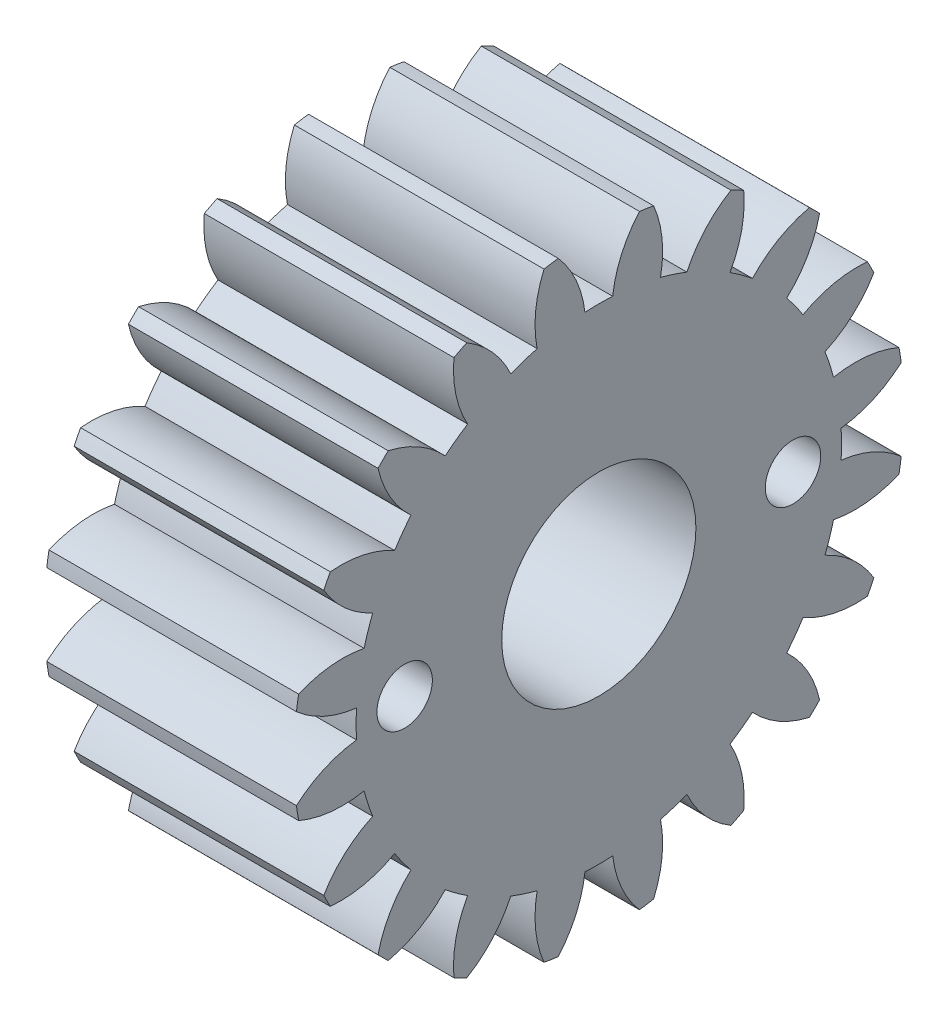
SolidWorks part; units mm, degrees
ref_plane "Plane1" through (0, 0, 0) normal (0, 0, 1) x (1, 0, 0)
ref_plane "Plane2" through (0, 0, 0) normal (0, 1, 0) x (1, 0, 0)
ref_plane "Plane3" through (0, 0, 0) normal (1, 0, 0) x (0, 0, -1)
other "Configuration Table"
sketch "HoldingSke" plane through (0, 0, 0) normal (0, 1, 0) x (1, 0, 0)
  line L0 (0, 0) -> (0.9397, -0.342)
  line L1 (-15, 0) -> (100, 0) construction
  line L2 (0, 0) -> (-2.1039, 2.3779)
  line L3 (0, 0) -> (-11.863, 4.5341)
  line L4 (0, 0) -> (8.1152, 2.9537)
  line L5 (0, 0) -> (-46.8476, -17.4728)
  line L6 (0, 0) -> (-4.1448, -2.7965)
  line L7 (-2.1039, 2.3779) -> (8.6586, 51.2059)
  line L8 (-76.2, 54.61) -> (-74.8, 54.61)
  line L9 (-71.009, 38.7566) -> (-53.1078, 45.2721)
  line L10 (-76.2, 71.12) -> (104.1128, 71.12)
  line L11 (0, 0) -> (-5, 0)
  line L12 (-76.2, 101.6) -> (-76.162, 101.6)
  line L13 (24.9733, 27.94) -> (52.9518, 28.4284)
  line L14 (24.9733, 27.94) -> (24.9743, 27.94)
  line L15 (24.9733, 27.94) -> (100.4006, 29.5858)
  line L16 (-63.627, -1) -> (-12.827, -1)
  circle A0 centre (0, 0) radius 4
  circle A1 centre (0, 0) radius 8.749
  circle A2 centre (0, 0) radius 37.5
  circle A3 centre (0, 0) radius 4
  dimension "MHD" = 17.498
  dimension "Hub_dia" = 75
  dimension "Bore" = 8
  dimension "MBD" = 8
  dimension "Num_teeth" = 20
  dimension "Pitch" = 1
  dimension "Overall_len" = 50
  dimension "Show_teeth" = 20
  dimension "Thickness" = 5
  dimension "OAL" = 50.0001
  dimension "T_dim" = 1.4
  dimension "Ap" = 20
  dimension "H" = 19.05
  dimension "Pitch_radius" = 180.3128
  dimension "Width" = 5
  dimension "Backlash" = 0.038
  dimension "Addendum_fac" = 1
  dimension "Dedendum_fac" = 1.25
  dimension "Clearance_fac" = 0.25
  dimension "Dedendum_add" = 0.001
  dimension "Module" = 1
sketch "BasProSke" plane through (0, 0, 0) normal (0, 1, 0) x (1, 0, 0)
  line L0 (-10, 0) -> (60, 0) construction
  line L1 (0, 0) -> (0, 11)
  line L2 (0, 0) -> (9, 0)
  line L3 (9, 0) -> (9, 11)
  line L4 (9, 11) -> (0, 11)
  dimension "Thickness" = 9
  dimension "Diameter" = 22
revolve "Base-Revolve" add sketch "BasProSke" angle 360 about L0
sketch "TooCutSke" plane through (0, 0, 0) normal (1, 0, 0) x (0, 0, -1)
  line L1 (0, 0) -> (0, 107) construction
  line L2 (0, 0) -> (-0.8511, 9.9637) construction
  line L3 (0, 0) -> (-3.1206, 19.7028) construction
  line L4 (-0.8511, 9.9637) -> (-1.5603, 9.8514) construction
  arc A0 (0.4999, 8.7347) -> (-0.4999, 8.7347) centre (0, 0) ccw
  arc A1 (1.4852, 10.9249) -> (-1.4852, 10.9249) centre (0, 0) ccw
  circle A2 centre (0, 0) radius 10 construction
  circle A3 centre (0, 0) radius 9.3969 construction
  arc A4 (-0.4999, 8.7347) -> (-1.4852, 10.9249) centre (-4.4722, 8.2645) ccw
  arc A5 (1.4852, 10.9249) -> (0.4999, 8.7347) centre (4.4722, 8.2645) ccw
  dimension "Root_dia" = 17.498
  dimension "Overcut_dia" = 22.0508
  dimension "Pitch_dia" = 20
  dimension "Base_dia" = 18.7939
  dimension "Flank_rad" = 4
  dimension "Half_ang" = 9
  dimension "Half_CT" = 0.7181
extrude "ToothCut" cut sketch "TooCutSke" along normal through all
fillet "Breaks" [suppressed] radius 0.02
fillet "RootFillets" [suppressed] radius 0.251
pattern_circular "TeethCuts" count 20 every 18 about axis through (-10, 0, 0) along (1, 0, 0) of "ToothCut", "RootFillets", "Breaks"
sketch "HubNeaOneSke" plane through (0, 0, 0) normal (-1, 0, 0) x (0, 0, 1)
  circle A0 centre (0, 0) radius 8.749
  dimension "Diameter" = 17.498
extrude "HubNearOne" [suppressed] add sketch "HubNeaOneSke" along normal blind 41.0001
sketch "HubNeaBotSke" plane through (0, 0, 0) normal (-1, 0, 0) x (0, 0, 1)
  circle A0 centre (0, 0) radius 8.749
  dimension "Diameter" = 17.498
extrude "HubNearBoth" [suppressed] add sketch "HubNeaBotSke" along normal blind 20.5
ref_plane "FarPln" through (9, 0, 0) normal (1, 0, 0) x (0, 0, -1)
sketch "HubFarSke" plane through (9, 0, 0) normal (1, 0, 0) x (0, 0, -1)
  circle A0 centre (0, 0) radius 8.749
  dimension "Diameter" = 17.498
extrude "HubFar" [suppressed] add sketch "HubFarSke" along normal blind 20.5
sketch "BorSke" plane through (0, 0, 0) normal (1, 0, 0) x (0, 0, -1)
  circle A0 centre (0, 0) radius 3.5
  dimension "Diameter" = 7
extrude "Bore" cut sketch "BorSke" along normal mid plane 100.0001
sketch "KeySke" plane through (0, 0, 0) normal (1, 0, 0) x (0, 0, -1)
  line L0 (-1.5, 0) -> (-1.5, 5.4)
  line L1 (-1.5, 5.4) -> (1.5, 5.4)
  line L2 (1.5, 5.4) -> (1.5, 0)
  line L3 (0, 0) -> (0, 34) construction
  line L4 (-1.5, 0) -> (1.5, 0)
  dimension "Offset" = 5.4
  dimension "Width" = 3
extrude "Keyway" [suppressed] cut sketch "KeySke" along normal mid plane 100.0001
pattern_circular "Keyway2" [suppressed] count 2 every 90 about axis through (-10, 0, 0) along (1, 0, 0)
sketch "Sketch1" plane through (9, 0, 0) normal (1, 0, 0) x (0, 0, -1)
  line L0 (-7, 0) -> (7, 0) construction
  circle A0 centre (-7, 0) radius 1
  circle A1 centre (7, 0) radius 1
  point P5 (0, 0)
  dimension "D1" = 2
  dimension "D2" = 2
extrude "Cut-Extrude1" cut sketch "Sketch1" against normal through all
equation "' \"Module@HoldingSke\" = 6.35"
equation "' \"Num_teeth@HoldingSke\" = 12"
equation "' \"Ap@HoldingSke\" =  20"
equation "' \"Ap@HoldingSke\" = 20"
equation "' \"Width@HoldingSke\" = 0.5 * 25.4"
equation "' \"Hub_dia@HoldingSke\"= 1 * 25.4"
equation "' \"Hub_dia@HoldingSke\" = 1 * 25.4"
equation "' \"Overall_len@HoldingSke\" = 1.0 * 25.4"
equation "' \"Bore@HoldingSke\" = 0.75 * 25.4"
equation "' \"T_dim@HoldingSke\" = 0.1 * 25.4"
equation "' \"Width@KeySke\" = 0.25 * 25.4"
equation "' \"Show_teeth@HoldingSke\" = 13"
equation "' \"Backlash@HoldingSke\" = 0.009 * 25.4"
equation "' \"Addendum_fac@HoldingSke\" = 1.0"
equation "' \"Dedendum_fac@HoldingSke\" = 1.25"
equation "' \"Dedendum_add@HoldingSke\" = 0.00005 * 25.4"
equation "' \"Clearance_fac@HoldingSke\" = 0.25"
equation "\"Pitch@HoldingSke\" = 1 / \"Module@HoldingSke\""
equation "\"Overcut_dia@TooCutSke\" = (\"Num_teeth@HoldingSke\" + 2 * \"Addendum_fac@HoldingSke\") / \"Pitch@HoldingSke\" + 0.002 * 25.4"
equation "\"Pitch_dia@TooCutSke\" = \"Num_teeth@HoldingSke\" / \"Pitch@HoldingSke\""
equation "\"Base_dia@TooCutSke\" = \"Num_teeth@HoldingSke\" / \"Pitch@HoldingSke\" * cos((\"Ap@HoldingSke\"  * 3.14159265 / 180))"
equation "\"Root_dia@TooCutSke\" = (\"Num_teeth@HoldingSke\" + 2) / \"Pitch@HoldingSke\" - 2 * (\"Addendum_fac@HoldingSke\" + \"Dedendum_fac@HoldingSke\") / \"Pitch@HoldingSke\" - \"Dedendum_add@HoldingSke\" * 2"
equation "\"Half_ang@TooCutSke\" = 180 / \"Num_teeth@HoldingSke\""
equation "\"Half_CT@TooCutSke\" = \"Num_teeth@HoldingSke\" / \"Pitch@HoldingSke\" * sin((3.14159265 / 2 / \"Num_teeth@HoldingSke\")) / 2 - 7 * \"Backlash@HoldingSke\" / 4"
equation "\"Flank_rad@TooCutSke\" = \"Num_teeth@HoldingSke\" / \"Pitch@HoldingSke\" / 5"
equation "\"Radius@RootFillets\" = \"Clearance_fac@HoldingSke\" / \"Pitch@HoldingSke\" + \"Dedendum_add@HoldingSke\""
equation "\"Break_rad@Breaks\" = 0.02 / \"Pitch@HoldingSke\""
equation "\"Thickness@HoldingSke\" = \"Width@HoldingSke\""
equation "\"OAL@HoldingSke\" = \"Thickness@HoldingSke\""
equation "\"MHD@HoldingSke\" = (\"Num_teeth@HoldingSke\" + 2) / \"Pitch@HoldingSke\" - 2 * (\"Addendum_fac@HoldingSke\" + \"Dedendum_fac@HoldingSke\")  / \"Pitch@HoldingSke\" - \"Dedendum_add@HoldingSke\" * 2"
equation "\"MBD@HoldingSke\" = (\"Num_teeth@HoldingSke\" + 2) / \"Pitch@HoldingSke\" - 2 * (\"Addendum_fac@HoldingSke\" + \"Dedendum_fac@HoldingSke\")  / \"Pitch@HoldingSke\" - \"Dedendum_add@HoldingSke\" * 2 - 0.002 * 25.4"
equation "\"MHD@HoldingSke\" = ((sgn( \"MHD@HoldingSke\" - \"Hub_dia@HoldingSke\" )-1)*( \"MHD@HoldingSke\" - \"Hub_dia@HoldingSke\" ))/-2+ \"Hub_dia@HoldingSke\""
equation "\"MBD@HoldingSke\" = ((sgn( \"MBD@HoldingSke\" - \"Bore@HoldingSke\" )-1)*( \"MBD@HoldingSke\" - \"Bore@HoldingSke\" ))/-2+ \"Bore@HoldingSke\""
equation "\"OAL@HoldingSke\" = ((sgn( \"OAL@HoldingSke\" - \"Overall_len@HoldingSke\" )+1)*( \"OAL@HoldingSke\" - \"Overall_len@HoldingSke\" ))/2 + \"Overall_len@HoldingSke\" + 0.000002 * 25.4"
equation "\"Num_teeth@TeethCuts\" = int( \"Show_teeth@HoldingSke\" ) + 1"
equation "\"Num_teeth@TeethCuts\" = ((sgn( \"Num_teeth@TeethCuts\" - \"Num_teeth@HoldingSke\" )-1)*( \"Num_teeth@TeethCuts\" - \"Num_teeth@HoldingSke\" ))/-2+ \"Num_teeth@HoldingSke\""
equation "\"Num_teeth@TeethCuts\" = ((sgn( \"Num_teeth@TeethCuts\" - 2.0)+1)*( \"Num_teeth@TeethCuts\" - 2.0))/2 +2.0"
equation "\"Angle@TeethCuts\" = 360.0 / \"Num_teeth@HoldingSke\""
equation "\"Diameter@BasProSke\" = (\"Num_teeth@HoldingSke\" + 2 * \"Addendum_fac@HoldingSke\") / \"Pitch@HoldingSke\""
equation "' \"Fillet_rad@BasProSke\" =  \"Thickness@HoldingSke\" * 0.05"
equation "' \"Fillet_rad@BasProSke\" = \"Thickness@HoldingSke\" * 0.05"
equation "\"MHD@HoldingSke\" = ((sgn( \"MHD@HoldingSke\" - \"Root_dia@TooCutSke\" )-1)*( \"MHD@HoldingSke\" - \"Root_dia@TooCutSke\" ))/-2+ \"Root_dia@TooCutSke\""
equation "\"Diameter@HubNeaOneSke\" = \"MHD@HoldingSke\""
equation "\"Length@HubNearOne\" = \"OAL@HoldingSke\" - \"Thickness@BasProSke\""
equation "\"Diameter@HubNeaBotSke\" = \"MHD@HoldingSke\""
equation "\"Length@HubNearBoth\" = ( \"OAL@HoldingSke\" - \"Thickness@BasProSke\" ) / 2.0"
equation "\"Thickness@FarPln\" = \"Thickness@BasProSke\""
equation "\"Diameter@HubFarSke\" = \"MHD@HoldingSke\""
equation "\"Length@HubFar\" = ( \"OAL@HoldingSke\" - \"Thickness@BasProSke\" ) / 2.0"
equation "\"D1@Bore\" = \"OAL@HoldingSke\" * 2.0"
equation "\"D1@Keyway\" = \"OAL@HoldingSke\" * 2.0"
equation "\"Offset@KeySke\" = \"T_dim@HoldingSke\" + \"MBD@HoldingSke\" / 2.0"
